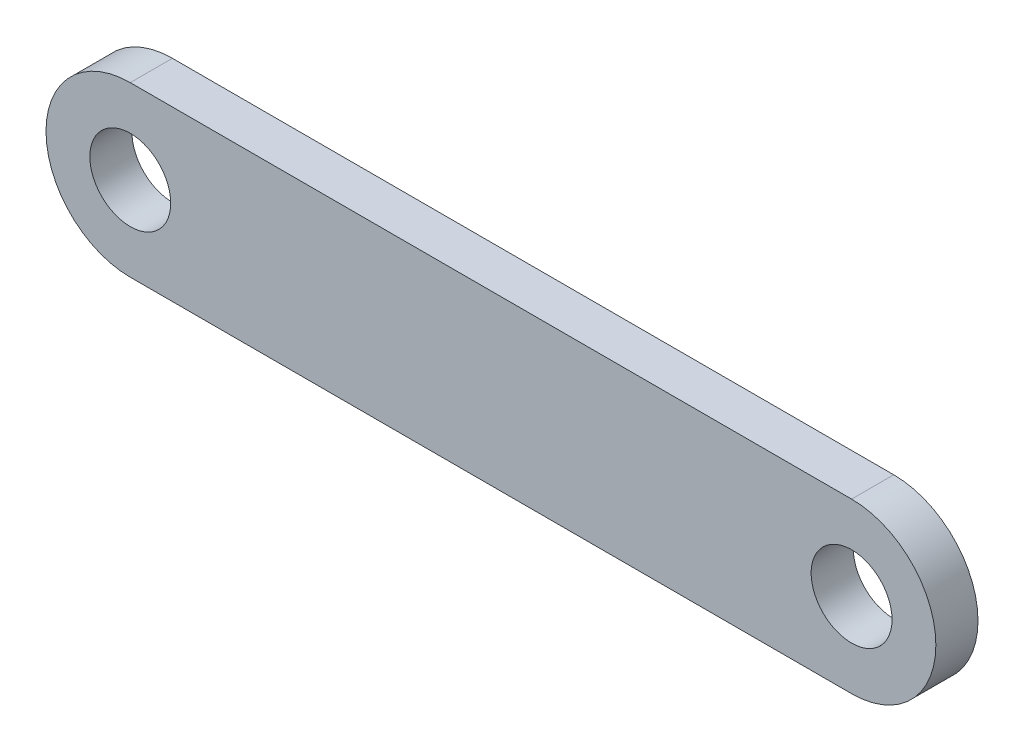
SolidWorks part; units mm, degrees
ref_plane "Front" through (0, 0, 0) normal (0, 0, 1) x (1, 0, 0)
ref_plane "Top" through (0, 0, 0) normal (0, 1, 0) x (1, 0, 0)
ref_plane "Right" through (0, 0, 0) normal (1, 0, 0) x (0, 0, -1)
sketch "Sketch1" plane through (0, 0, 0) normal (0, 0, 1) x (1, 0, 0)
  line L1 (-27.178, -6.35) -> (27.178, -6.35)
  line L2 (-27.178, -6.35) -> (-27.178, 6.35) construction
  line L3 (-27.178, 6.35) -> (27.178, 6.35)
  line L4 (27.178, -6.35) -> (27.178, 6.35) construction
  line L5 (-27.178, -6.35) -> (27.178, 6.35) construction
  line L6 (-27.178, 6.35) -> (27.178, -6.35) construction
  arc A0 (27.178, -6.35) -> (27.178, 6.35) centre (27.178, 0) ccw
  arc A1 (-27.178, 6.35) -> (-27.178, -6.35) centre (-27.178, 0) ccw
  circle A2 centre (27.178, 0) radius 3.048
  circle A3 centre (-27.178, 0) radius 3.048
  point P0 (0, 0)
  dimension "D3" = 6.096
  dimension "D4" = 6.096
  dimension "D1" = 12.7
  dimension "D2" = 54.356
extrude "Boss-Extrude1" add sketch "Sketch1" along normal blind 3.175
